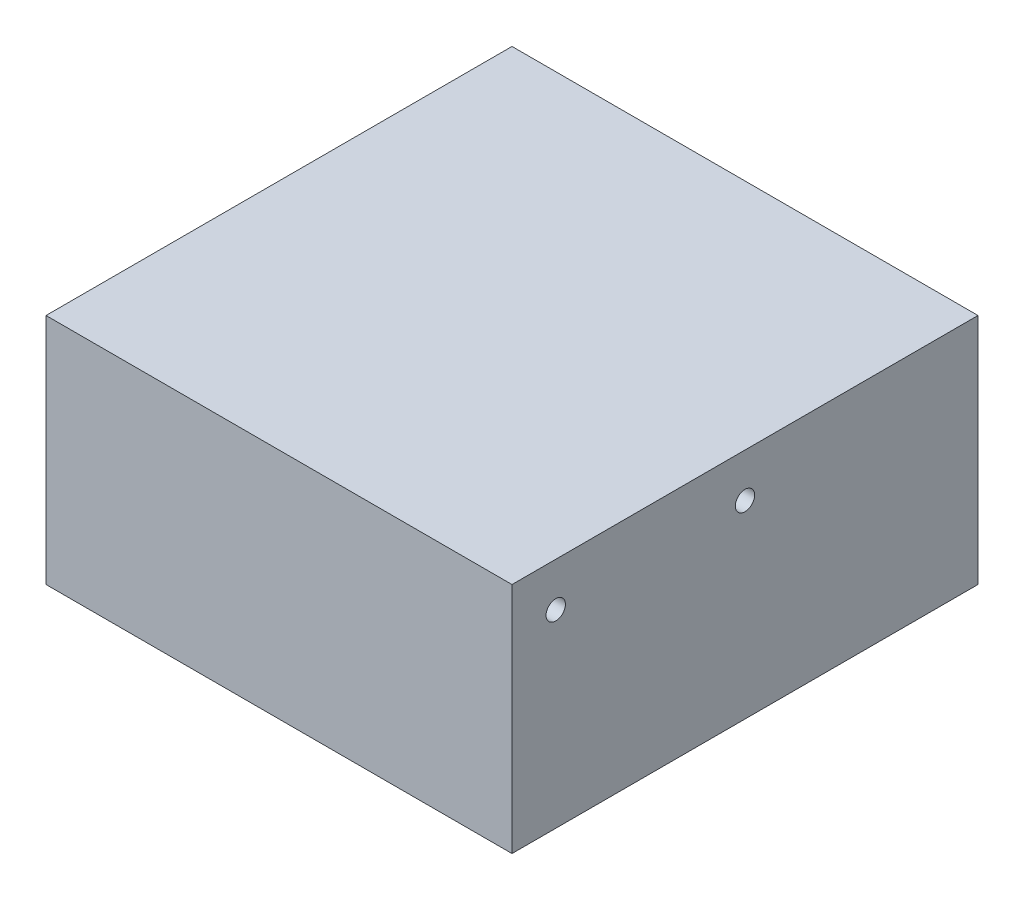
SolidWorks part; units mm, degrees
material "Refractory Clay"
ref_plane "Front Plane" through (0, 0, 0) normal (0, 0, 1) x (1, 0, 0)
ref_plane "Top Plane" through (0, 0, 0) normal (0, 1, 0) x (1, 0, 0)
ref_plane "Right Plane" through (0, 0, 0) normal (1, 0, 0) x (0, 0, -1)
sketch "Sketch1" plane through (0, 0, 0) normal (0, 1, 0) x (1, 0, 0)
  line L1 (-86, -86) -> (86, -86)
  line L2 (-86, -86) -> (-86, 86)
  line L3 (-86, 86) -> (86, 86)
  line L4 (86, -86) -> (86, 86)
  line L5 (-86, -86) -> (86, 86) construction
  line L6 (-86, 86) -> (86, -86) construction
  point P0 (0, 0)
  dimension "D1" = 172
  dimension "D2" = 172
extrude "Boss-Extrude1" add sketch "Sketch1" along normal blind 86
sketch "Sketch2" plane through (0, 0, 0) normal (0, 0, 1) x (1, 0, 0)
  line L0 (-86, 0) -> (86, 0) construction
  line L1 (0, 35) -> (0, -35) construction
  line L2 (0, 35) -> (0, 0)
  line L3 (0, 0) -> (35, 0)
  arc A0 (35, 0) -> (0, 35) centre (0, 0) ccw
  dimension "D1" = 35
revolve "Cut-Revolve1" cut sketch "Sketch2" angle 360 about L1
extrude "Cut-Extrude1" cut sketch "Sketch3" against normal through all both and the other way through all
sketch "Sketch3" plane through (0, 0, 0) normal (1, 0, 0) x (0, 0, -1)
  line L0 (0, -69.85) -> (0, 69.85) construction
  line L1 (0, 69.85) -> (-69.85, 69.85) construction
  line L2 (69.85, -69.85) -> (0, -69.85) construction
  circle A0 centre (0, -69.85) radius 3.5687
  circle A1 centre (-69.85, 69.85) radius 3.5687
  circle A2 centre (69.85, -69.85) radius 3.5687
  circle A3 centre (0, 69.85) radius 3.5687
